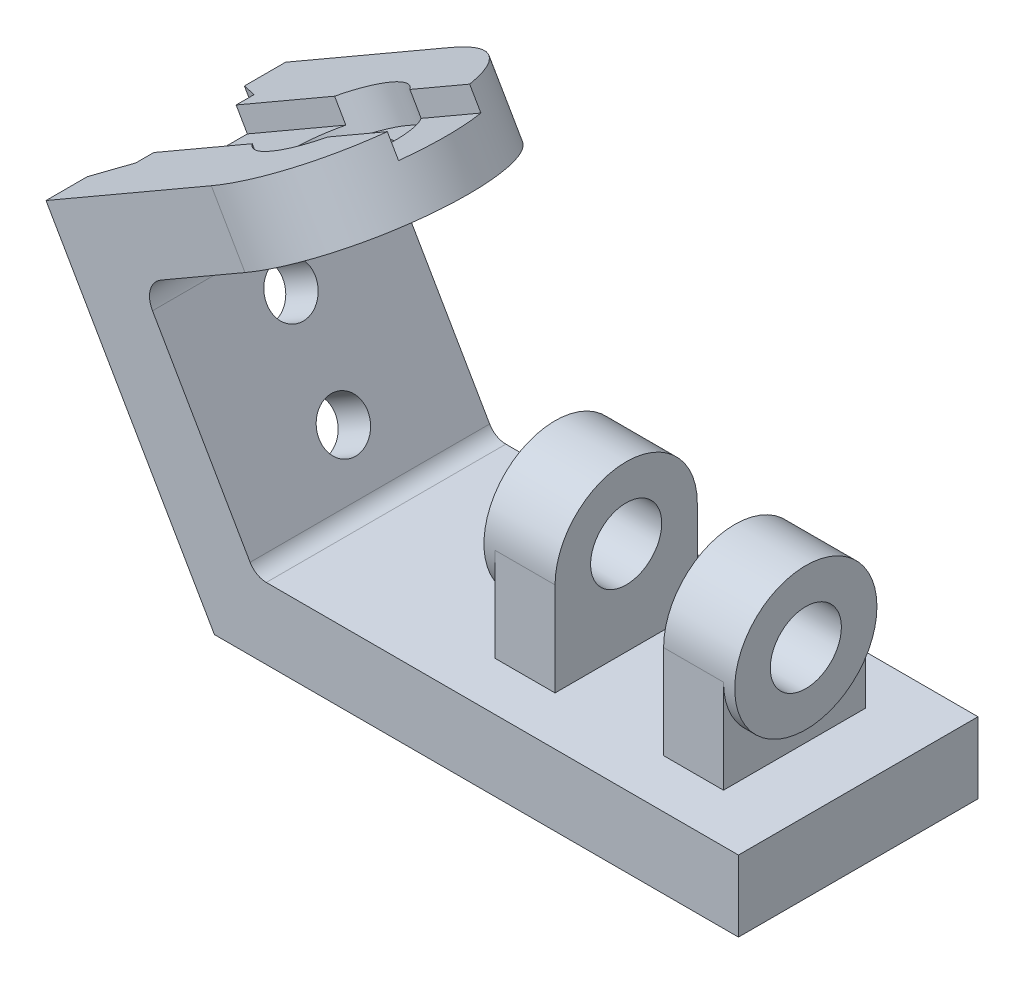
SolidWorks part; units mm, degrees
ref_plane "Front Plane" through (0, 0, 0) normal (0, 0, 1) x (1, 0, 0)
ref_plane "Top Plane" through (0, 0, 0) normal (0, 1, 0) x (1, 0, 0)
ref_plane "Right Plane" through (0, 0, 0) normal (1, 0, 0) x (0, 0, -1)
sketch "Sketch1" plane through (0, 0, 0) normal (0, 0, 1) x (1, 0, 0)
  line L0 (-70, -9.5) -> (-115, 68.4423)
  line L1 (-59.0303, 9.5) -> (70, 9.5)
  line L3 (-70, -9.5) -> (70, -9.5)
  line L4 (70, 9.5) -> (70, -9.5)
  line L5 (0, 0) -> (70, -9.5) construction
  line L6 (-70, -9.5) -> (70, 9.5) construction
  line L7 (-70, -9.5) -> (-168.4358, -9.5) construction
  line L8 (-59.0303, 9.5) -> (-98.5455, 77.9423)
  line L9 (-53.5455, 0) -> (-98.5455, 77.9423) construction
  line L10 (-115, 68.4423) -> (-98.5455, 77.9423)
  point P0 (0, 0)
  dimension "D1" = 140
  dimension "D2" = 19
  dimension "D3" = 60
  dimension "D4" = 90
  dimension "D5" = 19
extrude "Boss-Extrude1" add sketch "Sketch1" along normal blind 64
ref_plane "Plane1" through (-58.3864, 101.1282, 0) normal (-0.5, 0.866, 0) x (0.866, 0.5, 0)
sketch "Sketch2" plane through (-58.3864, 101.1282, 0) normal (-0.5, 0.866, 0) x (0.866, 0.5, 0)
  line L0 (-46.3718, 0) -> (-46.3718, -64)
  line L2 (-46.3718, -64) -> (-14.3718, -64)
  line L3 (-46.3718, 0) -> (-14.3718, 0)
  line L6 (65.3718, 0) -> (-46.3718, 0) construction
  line L7 (-46.3718, 0) -> (-65.3718, 0) construction
  arc A0 (-14.3718, -64) -> (-14.3718, 0) centre (-14.3718, -32) ccw
  circle A2 centre (-14.3718, -32) radius 9.5
  dimension "D2" = 64
  dimension "D4" = 19
extrude "Boss-Extrude3" add sketch "Sketch2" against normal blind 18
sketch "Sketch3" plane through (-58.3864, 101.1282, 0) normal (-0.5, 0.866, 0) x (0.866, 0.5, 0)
  line L0 (-65.3718, -32) -> (21.1099, -32) construction
  line L1 (-65.3718, -64) -> (-65.3718, 0) construction
  line L4 (-56.3718, -16.1962) -> (-56.3718, -47.8038)
  line L5 (-65.3718, -11) -> (-56.3718, -16.1962)
  line L6 (-65.3718, -53) -> (-56.3718, -47.8038)
  line L7 (-65.3718, -11) -> (-65.3718, -53)
  point P12 (-56.3718, -32)
extrude "Cut-Extrude1" cut sketch "Sketch3" against normal blind 128
sketch "Sketch4" plane through (-58.3864, 101.1282, 0) normal (-0.5, 0.866, 0) x (0.866, 0.5, 0)
  line L0 (-56.3718, -32) -> (22.3248, -32) construction
  line L1 (-56.3718, -47.8038) -> (-56.3718, -16.1962) construction
  line L3 (-60.0443, -21) -> (19.1661, -21)
  line L4 (-60.0443, -21) -> (-60.0443, -43)
  line L5 (-60.0443, -43) -> (19.1661, -43)
  line L6 (19.1661, -21) -> (19.1661, -43)
  line L7 (-60.0443, -21) -> (19.1661, -43) construction
  line L8 (-60.0443, -43) -> (19.1661, -21) construction
  point P4 (-20.4391, -32)
  dimension "D1" = 22
extrude "Cut-Extrude2" cut sketch "Sketch4" against normal blind 6
sketch "Sketch5" plane through (-58.3864, 101.1282, 0) normal (-0.5, 0.866, 0) x (0.866, 0.5, 0)
  circle A0 centre (-14.3718, -32) radius 16
  dimension "D1" = 32
extrude "Cut-Extrude4" cut sketch "Sketch5" against normal blind 9
ref_plane "Plane2" through (-48.8194, -28.1859, 0) normal (-0.866, -0.5, 0) x (0, 0, 1)
sketch "Sketch6" plane through (-48.8194, -28.1859, 0) normal (-0.866, -0.5, 0) x (0, 0, 1)
  line L0 (32, 110.7728) -> (32, 21.5766) construction
  line L1 (21, 110.7728) -> (43, 110.7728) construction
  line L2 (47.8038, 21.5766) -> (16.1962, 21.5766) construction
  circle A0 centre (32, 82.7728) radius 6.5
  circle A1 centre (32, 54.7728) radius 6.5
  dimension "D2" = 13
  dimension "D4" = 13
  dimension "D1" = 28
  dimension "D3" = 28
extrude "Cut-Extrude6" cut sketch "Sketch6" against normal up to surface (10 mm away) up to face at (-74.2879, 35.9269, 32)
fillet "Fillet1" radius 5 1 edges at (-59.0303, 9.5, 32)
fillet "Fillet2" radius 6 1 edges at (-89.5455, 62.3538, 32)
ref_plane "Plane3" through (0, 9.5, 0) normal (0, 1, 0) x (1, 0, 0)
sketch "Sketch7" plane through (0, 9.5, 0) normal (0, 1, 0) x (1, 0, 0)
  line L5 (37, -13) -> (53, -13)
  line L6 (37, -13) -> (37, -51)
  line L7 (37, -51) -> (53, -51)
  line L8 (53, -13) -> (53, -51)
  point P4 (44.9497, -32)
  dimension "D1" = 16
  dimension "D4" = 38
extrude "Boss-Extrude4" add sketch "Sketch7" along normal blind 25
ref_plane "Plane4" through (56, 0, 0) normal (1, 0, 0) x (0, 0, -1)
sketch "Sketch8" plane through (56, 0, 0) normal (1, 0, 0) x (0, 0, -1)
  line L0 (-51, 34.5) -> (-13, 34.5) construction
  circle A0 centre (-32, 34.5) radius 19
  circle A1 centre (-32, 34.5) radius 9.5
  dimension "D1" = 38
  dimension "D2" = 19
extrude "Boss-Extrude5" add sketch "Sketch8" against normal blind 19
sketch "Sketch9" plane through (56, 0, 0) normal (1, 0, 0) x (0, 0, -1)
  line L0 (-41.5, 34.5) -> (-22.5, 34.5) construction
  circle A0 centre (-32, 34.5) radius 9.5
extrude "Cut-Extrude7" cut sketch "Sketch9" against normal blind 19
sketch "Sketch10" plane through (0, 9.5, 0) normal (0, 1, 0) x (1, 0, 0)
  line L0 (37, -32) -> (22.5, -32)
  line L1 (37, -13) -> (37, -51) construction
  line L2 (22.5, -1.1959) -> (22.5, -62.8041) construction
  point P7 (22.5, -32)
  dimension "D1" = 14.5
ref_plane "Plane5" through (22.5, 0, 0) normal (1, 0, 0) x (0, 0, -1)
mirror "Mirror1" about plane through (22.5, 0, 0) normal (1, 0, 0) of "Boss-Extrude5", "Boss-Extrude4"
sketch "Sketch11" plane through (-11, 0, 0) normal (-1, 0, 0) x (0, 0, 1)
  circle A0 centre (32, 34.5) radius 9.5
extrude "Cut-Extrude8" cut sketch "Sketch11" against normal blind 19
